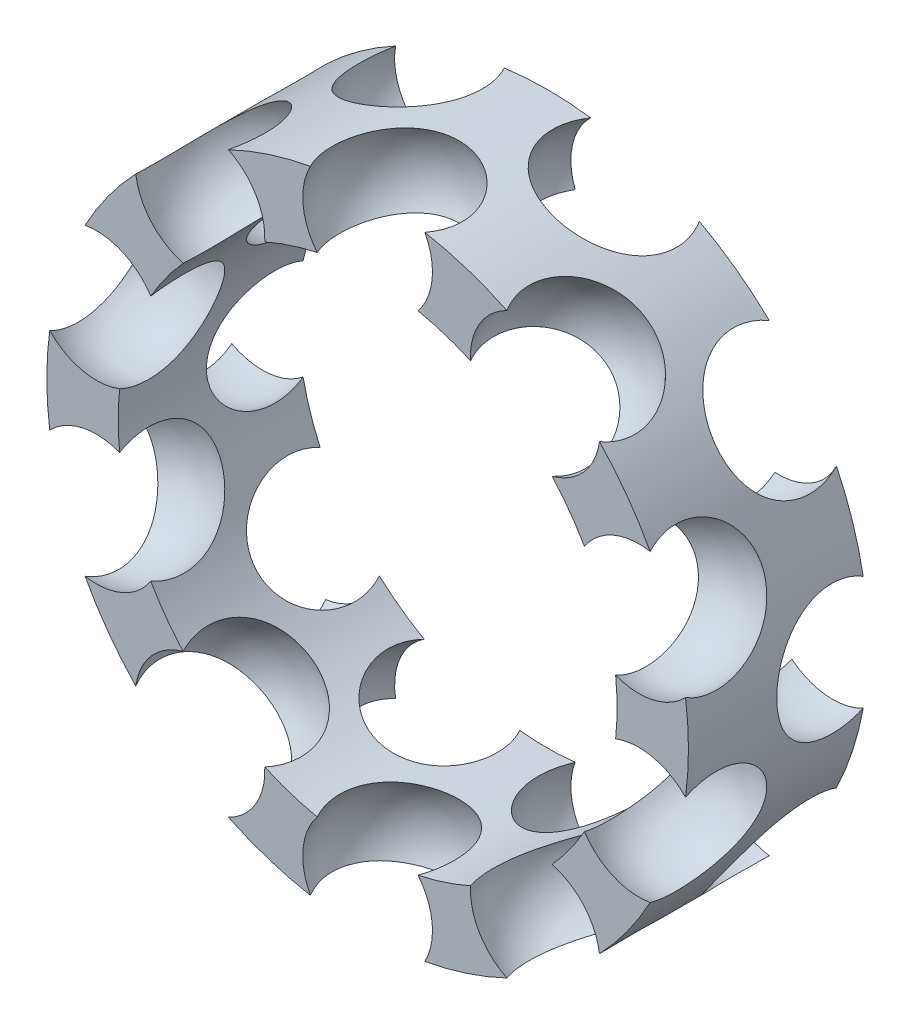
SolidWorks part; units mm, degrees
material "Простая углеродистая сталь"
ref_plane "Спереди" through (0, 0, 0) normal (0, 0, 1) x (1, 0, 0)
ref_plane "Сверху" through (0, 0, 0) normal (0, 1, 0) x (1, 0, 0)
ref_plane "Справа" through (0, 0, 0) normal (1, 0, 0) x (0, 0, -1)
sketch "Эскиз1" plane through (0, 0, 0) normal (1, 0, 0) x (0, 0, -1)
  line L0 (0, 0) -> (50000, 0) construction
  line L1 (0, 7.3125) -> (4.5, 7.3125)
  line L2 (0, 7.3125) -> (0, 5.6875)
  line L3 (0, 5.6875) -> (4.5, 5.6875)
  line L4 (4.5, 7.3125) -> (4.5, 5.6875)
  dimension "D1" = 4.5
  dimension "D2" = 5.6875
  dimension "D3" = 7.3125
revolve "Повернуть1" add sketch "Эскиз1" angle 360 about L0
ref_plane "Плоскость1" through (0, 6.5, 0) normal (0, 1, 0) x (1, 0, 0)
sketch "Эскиз2" plane through (0, 6.5, 0) normal (0, 1, 0) x (1, 0, 0)
  line L0 (0, 2.5) -> (0, -0.75)
  arc A0 (0, -0.75) -> (0, 2.5) centre (0, 0.875) ccw
  dimension "D1" = 3.25
  dimension "D2" = 0.875
revolve "Вырез-Повернуть1" cut sketch "Эскиз2" angle 360 about L0
pattern_circular "Круговой массив1" count 10 over 360 about axis through (0, 0, 0) along (0, 0, 1) of "Вырез-Повернуть1"
ref_plane "Плоскость2" through (-2.2597, 6.9546, 0) normal (-0.309, 0.9511, 0) x (0, 0, 1)
ref_plane "Плоскость3" through (-2.0086, 6.1819, 0) normal (-0.309, 0.9511, 0) x (0, 0, 1)
sketch "Эскиз3" plane through (-2.0086, 6.1819, 0) normal (-0.309, 0.9511, 0) x (0, 0, 1)
  line L0 (-4.5, 7.3125) -> (-4.5, -7.3125) construction
  line L1 (-5.245, 0) -> (-1.995, 0)
  arc A0 (-1.995, 0) -> (-5.245, 0) centre (-3.62, 0) ccw
  dimension "D1" = 3.25
  dimension "D2" = 0.88
revolve "Вырез-Повернуть2" cut sketch "Эскиз3" angle 360 about L1
pattern_circular "Круговой массив2" count 10 over 360 about axis through (0, 0, 0) along (0, 0, 1) of "Вырез-Повернуть2"
sketch "Эскиз4" plane through (0, 0, 0) normal (0, 0, 1) x (1, 0, 0)
  circle A0 centre (0, 0) radius 7.3125
  dimension "D1" = 14.625
extrude "Вырез-Вытянуть1" cut sketch "Эскиз4" against normal blind 0.2
ref_plane "Плоскость4" through (0, 0, -2.25) normal (0, 0, 1) x (1, 0, 0)
mirror "Зеркальное отражение1" about plane through (0, 0, -2.25) normal (0, 0, 1) of "Вырез-Вытянуть1"
